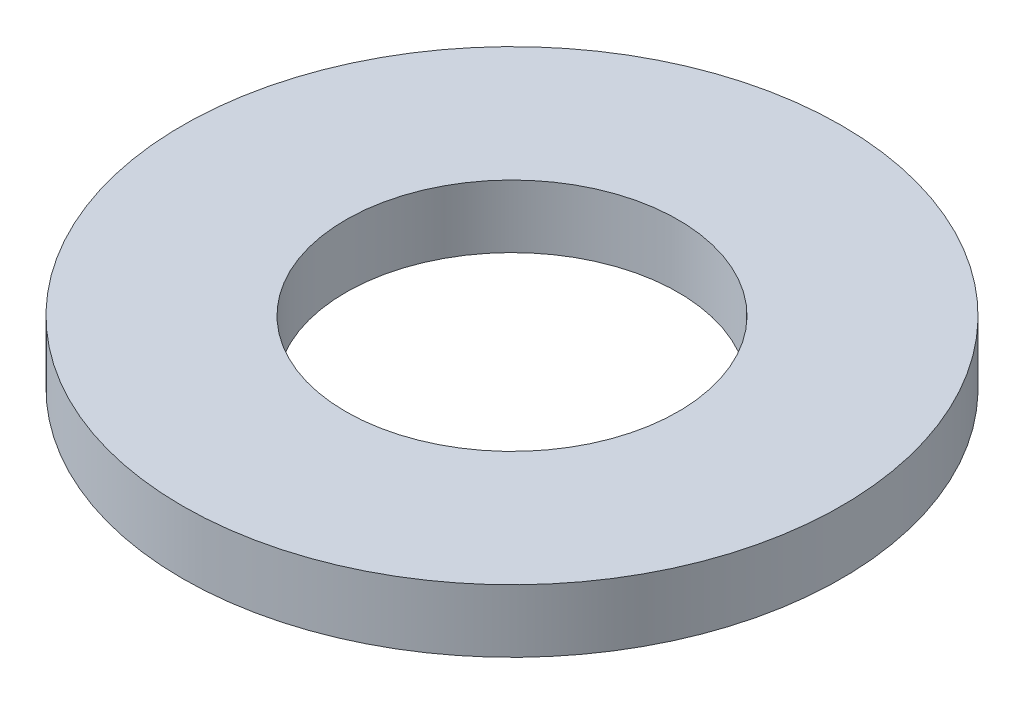
SolidWorks part; units mm, degrees
material "Plain Carbon Steel"
ref_plane "Front Plane" through (0, 0, 0) normal (0, 0, 1) x (1, 0, 0)
ref_plane "Top Plane" through (0, 0, 0) normal (0, 1, 0) x (1, 0, 0)
ref_plane "Right Plane" through (0, 0, 0) normal (1, 0, 0) x (0, 0, -1)
sketch "Sketch1" plane through (0, 0, 0) normal (0, 1, 0) x (1, 0, 0)
  circle A0 centre (0, 0) radius 4.4323
  circle A1 centre (0, 0) radius 8.7884
  dimension "D1" = 17.5768
  dimension "D2" = 8.8646
extrude "Boss-Extrude1" add sketch "Sketch1" along normal mid plane 1.6764
